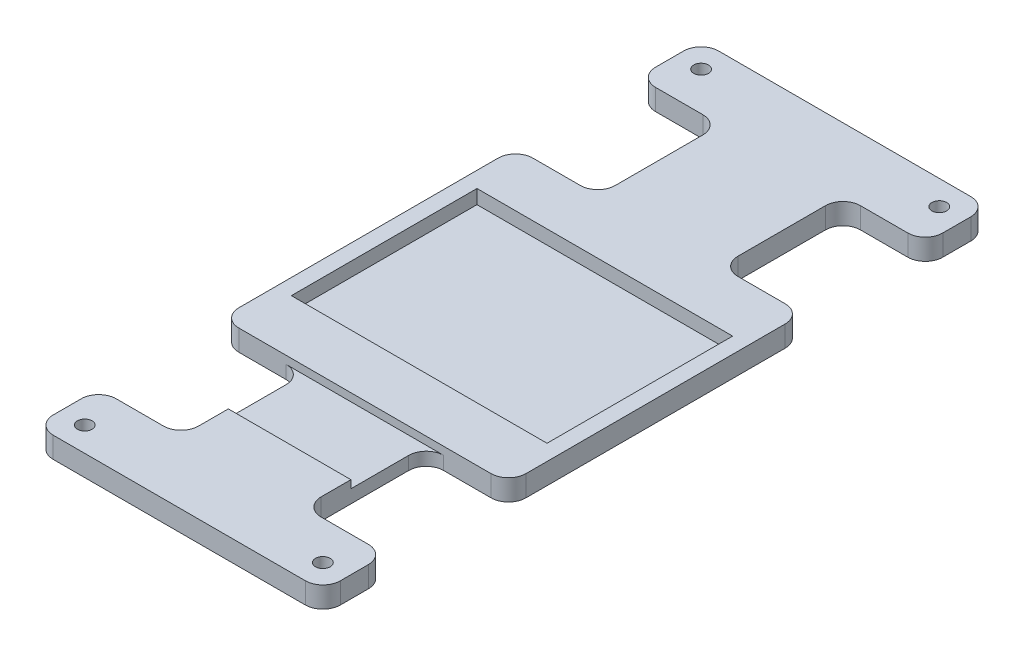
SolidWorks part; units mm, degrees
ref_plane "Front Plane" through (0, 0, 0) normal (0, 0, 1) x (1, 0, 0)
ref_plane "Top Plane" through (0, 0, 0) normal (0, 1, 0) x (1, 0, 0)
ref_plane "Right Plane" through (0, 0, 0) normal (1, 0, 0) x (0, 0, -1)
sketch "Sketch1" plane through (0, 0, 0) normal (0, 1, 0) x (1, 0, 0)
  line L1 (-42.5, -95) -> (42.5, -95)
  line L2 (-42.5, -95) -> (-42.5, 95)
  line L3 (-42.5, 95) -> (42.5, 95)
  line L4 (42.5, -95) -> (42.5, 95)
  line L5 (-42.5, -95) -> (42.5, 95) construction
  line L6 (-42.5, 95) -> (42.5, -95) construction
  point P0 (0, 0)
  dimension "D1" = 190
  dimension "D2" = 85
extrude "Boss-Extrude1" add sketch "Sketch1" along normal blind 6
sketch "Sketch2" plane through (0, 6, 0) normal (0, 1, 0) x (1, 0, 0)
  line L1 (-36.5, 26.5) -> (36.5, 26.5)
  line L2 (-36.5, 26.5) -> (-36.5, -26.5)
  line L3 (-36.5, -26.5) -> (36.5, -26.5)
  line L4 (36.5, 26.5) -> (36.5, -26.5)
  line L5 (-36.5, 26.5) -> (36.5, -26.5) construction
  line L6 (-36.5, -26.5) -> (36.5, 26.5) construction
  line L8 (-42.5, -95) -> (42.5, -95) construction
  line L9 (0, 22.5124) -> (0, -48.4798) construction
  dimension "D1" = 73
  dimension "D2" = 53
  dimension "D3" = 68.5
  dimension "D4" = 36.5
extrude "Cut-Extrude1" cut sketch "Sketch2" against normal blind 4
sketch "Sketch3" plane through (0, 6, 0) normal (0, 1, 0) x (1, 0, 0)
  line L0 (42.5, -95) -> (42.5, 95) construction
  line L1 (-42.5, -95) -> (42.5, -95) construction
  line L2 (32.1231, 0) -> (-76.428, 0) construction
  line L3 (0, -58.0279) -> (0, 41.0495) construction
  circle A0 centre (34, -88) radius 2.1
  circle A1 centre (-34, -88) radius 2.1
  circle A2 centre (-34, 88) radius 2.1
  circle A3 centre (34, 88) radius 2.1
  dimension "D1" = 8.5
  dimension "D2" = 7
extrude "Cut-Extrude2" cut sketch "Sketch3" against normal blind 9
sketch "Sketch4" plane through (0, 6, 0) normal (0, 1, 0) x (1, 0, 0)
  line L0 (-42.5, -95) -> (42.5, -95) construction
  line L5 (0, 0) -> (68.7943, 0) construction
  line L6 (-42.5, 77) -> (-17.5, 77)
  line L7 (-42.5, 95) -> (-42.5, -95) construction
  line L8 (-42.5, -42) -> (-17.5, -42)
  line L9 (-42.5, -42) -> (-42.5, -77)
  line L10 (-42.5, -77) -> (-17.5, -77)
  line L11 (-17.5, -42) -> (-17.5, -77)
  line L12 (0, 0) -> (0, 119.7231) construction
  line L13 (-17.5, 42) -> (-17.5, 77)
  line L14 (42.5, -77) -> (17.5, -77)
  line L15 (17.5, -42) -> (17.5, -77)
  line L16 (42.5, -42) -> (17.5, -42)
  line L17 (42.5, -42) -> (42.5, -77)
  line L18 (-42.5, 42) -> (-17.5, 42)
  line L20 (-42.5, 42) -> (-42.5, 77)
  line L21 (42.5, 42) -> (42.5, 77)
  line L22 (42.5, 42) -> (17.5, 42)
  line L23 (17.5, 42) -> (17.5, 77)
  line L24 (42.5, 77) -> (17.5, 77)
  dimension "D4" = 17.5
  dimension "D5" = 35
  dimension "D6" = 18
extrude "Cut-Extrude3" cut sketch "Sketch4" against normal blind 10
sketch "Sketch5" plane through (0, 6, 0) normal (0, 1, 0) x (1, 0, 0)
  line L0 (-42.5, -95) -> (42.5, -95) construction
  line L1 (-42.5, 95) -> (-41, 95)
  line L2 (-42.5, 95) -> (-42.5, -95)
  line L3 (-42.5, -95) -> (-41, -95)
  line L4 (-41, 95) -> (-41, -95)
  line L5 (0, 0) -> (0, -59.4569) construction
  line L6 (42.5, -95) -> (41, -95)
  line L7 (42.5, 95) -> (42.5, -95)
  line L8 (42.5, 95) -> (41, 95)
  line L9 (41, 95) -> (41, -95)
  dimension "D1" = 1.5
extrude "Cut-Extrude4" cut sketch "Sketch5" against normal blind 10
sketch "Sketch6" plane through (0, 6, 0) normal (0, 1, 0) x (1, 0, 0)
  line L0 (17.5, -42) -> (17.5, -77) construction
  line L1 (17.5, -42) -> (-17.5, -42)
  line L2 (17.5, -42) -> (17.5, -63.5)
  line L3 (17.5, -63.5) -> (-17.5, -63.5)
  line L4 (-17.5, -42) -> (-17.5, -63.5)
  line L5 (-17.5, -77) -> (-17.5, -42) construction
  line L6 (-41, -95) -> (41, -95) construction
  dimension "D1" = 21.5
  dimension "D2" = 31.5
extrude "Cut-Extrude5" cut sketch "Sketch6" against normal blind 2.25
fillet "Fillet1" radius 5 20 edges at (-17.5, 1.875, 42) (17.5, 1.875, 42) (17.5, 3, 77) (-17.5, 3, 77) (-41, 3, 77) (-41, 3, 42) (-41, 3, -42) (-41, 3, -77) (41, 3, 77) (41, 3, 42) (41, 3, -42) (41, 3, -77) (-17.5, 3, -77) (-17.5, 3, -42) (17.5, 3, -77) (17.5, 3, -42) (41, 3, 95) (-41, 3, 95) (41, 3, -95) (-41, 3, -95)
